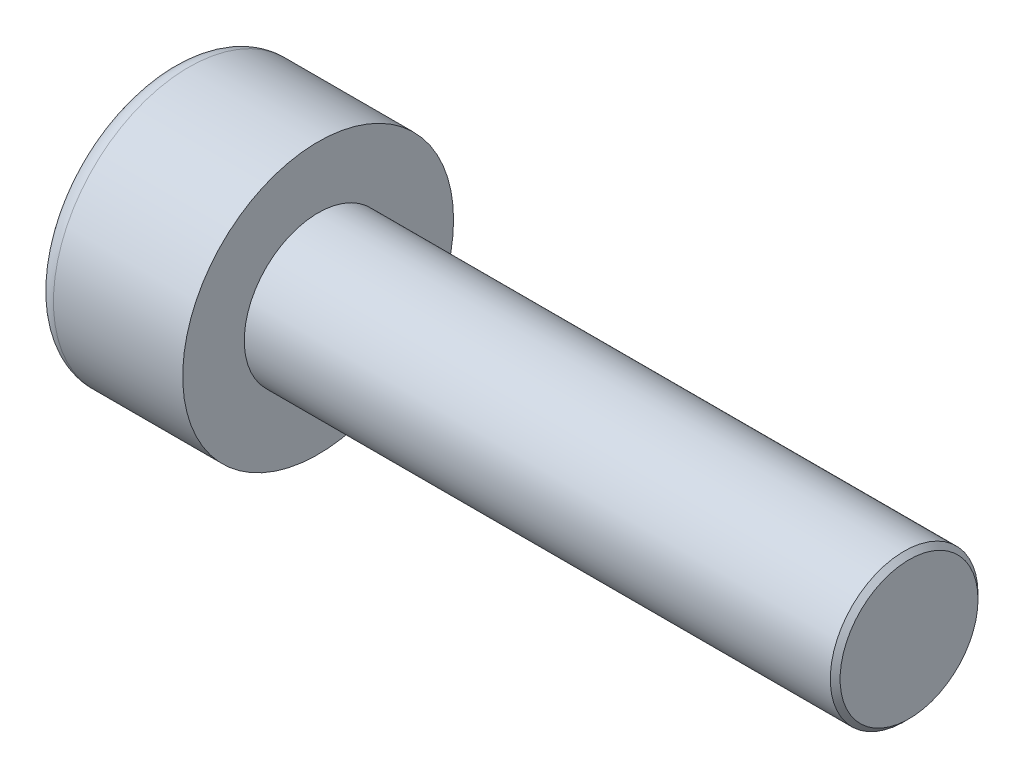
SolidWorks part; units mm, degrees
ref_plane "Front" through (0, 0, 0) normal (0, 0, 1) x (1, 0, 0)
ref_plane "Top" through (0, 0, 0) normal (0, 1, 0) x (1, 0, 0)
ref_plane "Right" through (0, 0, 0) normal (1, 0, 0) x (0, 0, -1)
sketch "Sketch1" plane through (0, 0, 0) normal (1, 0, 0) x (0, 0, -1)
  circle A0 centre (0, 0) radius 2.75
  dimension "dk" = 5.5
extrude "BaseHead" add sketch "Sketch1" along normal blind 3
sketch "Sketch2" plane through (3, 0, 0) normal (1, 0, 0) x (0, 0, -1)
  circle A0 centre (0, 0) radius 1.5
  dimension "d" = 3
extrude "BaseBody" add sketch "Sketch2" along normal blind 12
cosmetic thread "ThreadCosmetic1" [suppressed] parameters "b"=12, "D2"=2.459
sketch "Sketch3" plane through (0, 0, 0) normal (1, 0, 0) x (0, 0, -1)
  line L1 (1.4434, 0) -> (0.7217, 1.25)
  line L2 (0.7217, 1.25) -> (-0.7217, 1.25)
  line L3 (-0.7217, 1.25) -> (-1.4434, 0)
  line L4 (-1.4434, 0) -> (-0.7217, -1.25)
  line L5 (-0.7217, -1.25) -> (0.7217, -1.25)
  line L6 (0.7217, -1.25) -> (1.4434, 0)
  circle A0 centre (0, 0) radius 1.25 construction
  dimension "s" = 2.5
  dimension "e" = 2.8868
extrude "HexagonSocket" cut sketch "Sketch3" along normal blind 1.3
sketch "Sketch4" plane through (-4.1961, 0.75, 0) normal (0, 0, 1) x (-1, 0, 0)
  line L0 (-5.4961, 2) -> (-6.2178, 0.75)
  line L2 (-6.2178, 0.75) -> (-5.4961, 0.75)
  line L3 (-5.4961, 0.75) -> (-5.4961, 2)
  line L4 (-5.0351, 0.75) -> (0.839, 0.75) construction
  line L5 (-19.1961, 0.75) -> (-7.1961, 0.75) construction
  line L6 (-7.1961, 0.75) -> (-4.1961, 0.75) construction
  dimension "m" = 60
revolve "Cut-Revolve1" cut sketch "Sketch4" angle 360 about L4
fillet "HeadFillet" [suppressed] radius 0.1
fillet "TopFillet" radius 0.375 1 edges at (0, 0, -2.75)
chamfer "Chamfer1" distance 0.1 angle 45 1 edges at (15, 0, -1.5)
sketch "Sketch5" plane through (0, 0, 0) normal (0, 0, 1) x (1, 0, 0)
  line L0 (14.9, 1.2657) -> (15.0352, 1.5)
  line L1 (15.0352, 1.5) -> (15.0352, 1.7705)
  line L2 (15.0352, 1.7705) -> (14.7647, 1.7705)
  line L3 (14.7647, 1.7705) -> (14.7647, 1.5)
  line L4 (14.7647, 1.5) -> (14.9, 1.2657)
  line L5 (0, 0) -> (7.8886, 0) construction
  line L6 (14.9, -1.5) -> (14.9, 1.5) construction
  dimension "D1" = 3
  dimension "D2" = 0.2705
revolve "Cut-Revolve10" [suppressed] cut sketch "Sketch5" angle 360 about L5
pattern_linear "LPattern10" [suppressed] count 37 spacing 0.3246 along (1, 0, 0)
equation "\"r1@TopFillet\" = \"d@Sketch2\" / 8"
equation "\"D1@Chamfer1\" = \"r@HeadFillet\""
equation "\"D1@Sketch5\" = \"d@Sketch2\""
equation "\"D2@Sketch5\" =  ( \"d@Sketch2\" - \"D2@ThreadCosmetic1\" )  / 2"
equation "\"D3@LPattern10\" = \"D2@Sketch5\" * 1.2"
equation "\"D1@LPattern10\" = \"b@ThreadCosmetic1\" / \"D3@LPattern10\""
